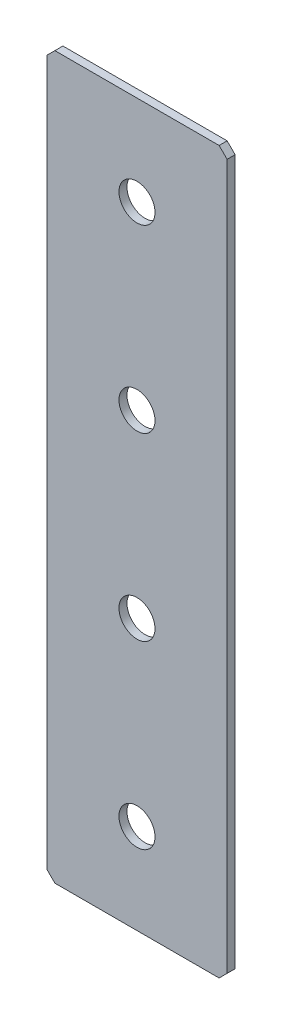
SolidWorks part; units mm, degrees
material "Простая углеродистая сталь"
ref_plane "Спереди(Плоскость XY)" through (0, 0, 0) normal (0, 0, 1) x (1, 0, 0)
ref_plane "Сверху(Плоскость XZ)" through (0, 0, 0) normal (0, 1, 0) x (1, 0, 0)
ref_plane "Справа(Плоскость ZY)" through (0, 0, 0) normal (1, 0, 0) x (0, 0, -1)
sketch "Эскиз1" plane through (0, 0, 0) normal (0, 0, 1) x (1, 0, 0)
  line L1 (-22.5, -90) -> (22.5, -90)
  line L2 (-22.5, -90) -> (-22.5, 90)
  line L3 (-22.5, 90) -> (22.5, 90)
  line L4 (22.5, -90) -> (22.5, 90)
  line L5 (-22.5, -90) -> (22.5, 90) construction
  line L6 (-22.5, 90) -> (22.5, -90) construction
  point P0 (0, 0)
  dimension "D1" = 45
  dimension "D2" = 180
extrude "Бобышка-Вытянуть1" add sketch "Эскиз1" along normal blind 2
chamfer "Фаска1" distance 2 angle 45 4 edges at (-22.5, -90, 1) (22.5, -90, 1) (-22.5, 90, 1) (22.5, 90, 1)
hole_wizard "Отверстие с зазором M81" positions "Эскиз2" profile "Эскиз3" hole size "M8" standard "DIN" end condition through all
sketch "Эскиз2" plane through (0, 0, 2) normal (0, 0, 1) x (1, 0, 0)
  line L15 (0, 22.5) -> (0, 67.5) construction
  line L17 (0, 22.5) -> (0, -22.5) construction
  line L18 (0, -22.5) -> (0, -67.5) construction
  point P204 (0, 67.5)
  point P206 (0, 22.5)
  point P208 (0, -22.5)
  point P210 (0, -67.5)
  dimension "D2" = 45
sketch "Эскиз3" plane through (0, 67.5, 2) normal (1, 0, 0) x (0, -1, 0)
  line L0 (0, 0) -> (0, 2)
  line L1 (0, 2) -> (4.5, 2)
  line L2 (4.5, 2) -> (4.5, 0)
  line L5 (4.5, 0) -> (0, 0)
  line L11 (0, -6.35) -> (0, 107.95) construction
  dimension "Диаметр сквозного отверстия" = 9
  dimension "Глубина сквозного отверстия" = 2
